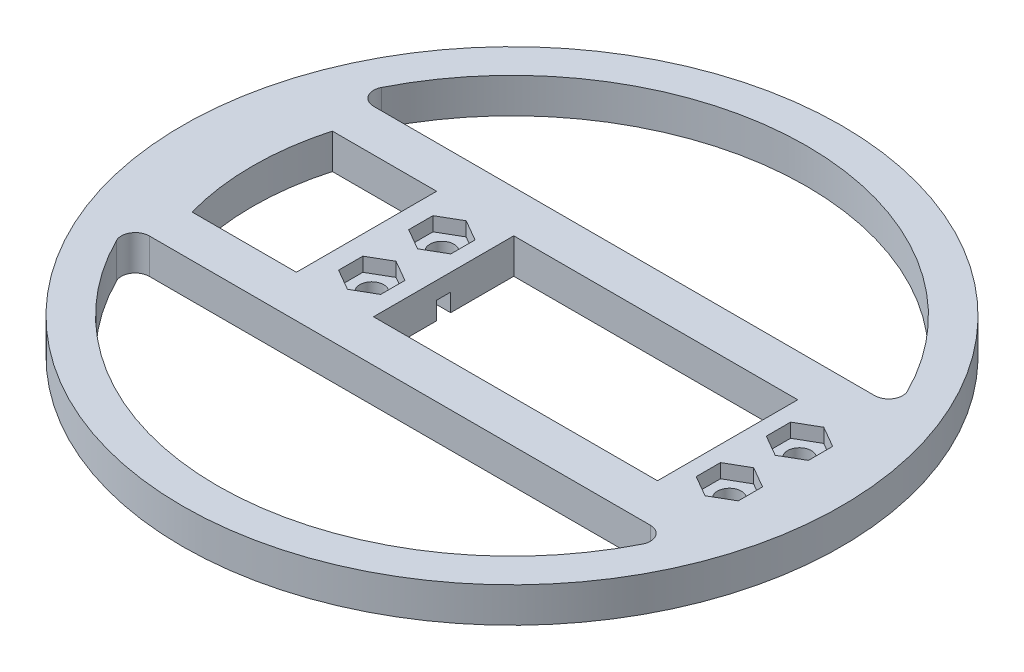
SolidWorks part; units mm, degrees
ref_plane "Front" through (0, 0, 0) normal (0, 0, 1) x (1, 0, 0)
ref_plane "Top" through (0, 0, 0) normal (0, 1, 0) x (1, 0, 0)
ref_plane "Right" through (0, 0, 0) normal (1, 0, 0) x (0, 0, -1)
sketch "Эскиз1" plane through (0, 0, 0) normal (0, 1, 0) x (1, 0, 0)
  line L0 (-47, 0) -> (47, 0) construction
  line L1 (10.5, 10) -> (10.5, -10) construction
  line L2 (-9.75, 10) -> (30.75, 10)
  line L3 (-9.75, 10) -> (-9.75, -10)
  line L4 (-9.75, -10) -> (30.75, -10)
  line L5 (30.75, 10) -> (30.75, -10)
  circle A0 centre (0, 0) radius 47
  circle A1 centre (-15, 5) radius 1.7
  circle A2 centre (-15, -5) radius 1.7
  circle A3 centre (36, 5) radius 1.7
  circle A4 centre (36, -5) radius 1.7
  dimension "D1" = 94
  dimension "D7" = 3.4
  dimension "D2" = 20
  dimension "D3" = 40.5
  dimension "D4" = 9.75
  dimension "D5" = 10
  dimension "D6" = 51
extrude "Бобышка-Вытянуть1" add sketch "Эскиз1" along normal blind 5
sketch "Эскиз2" plane through (0, 5, 0) normal (0, 1, 0) x (1, 0, 0)
  line L1 (-12, 6.7321) -> (-15, 8.4641)
  line L2 (-15, 8.4641) -> (-18, 6.7321)
  line L3 (-18, 6.7321) -> (-18, 3.2679)
  line L4 (-18, 3.2679) -> (-15, 1.5359)
  line L5 (-15, 1.5359) -> (-12, 3.2679)
  line L6 (-12, 3.2679) -> (-12, 6.7321)
  line L7 (-12, -3.2679) -> (-15, -1.5359)
  line L8 (-15, -1.5359) -> (-18, -3.2679)
  line L9 (-18, -3.2679) -> (-18, -6.7321)
  line L10 (-18, -6.7321) -> (-15, -8.4641)
  line L11 (-15, -8.4641) -> (-12, -6.7321)
  line L12 (-12, -6.7321) -> (-12, -3.2679)
  line L13 (36, 8.4641) -> (33, 6.7321)
  line L14 (33, 6.7321) -> (33, 3.2679)
  line L15 (33, 3.2679) -> (36, 1.5359)
  line L16 (36, 1.5359) -> (39, 3.2679)
  line L17 (39, 3.2679) -> (39, 6.7321)
  line L18 (39, 6.7321) -> (36, 8.4641)
  line L19 (36, -1.5359) -> (33, -3.2679)
  line L20 (33, -3.2679) -> (33, -6.7321)
  line L21 (33, -6.7321) -> (36, -8.4641)
  line L22 (36, -8.4641) -> (39, -6.7321)
  line L23 (39, -6.7321) -> (39, -3.2679)
  line L24 (39, -3.2679) -> (36, -1.5359)
  circle A0 centre (-15, 5) radius 3 construction
  circle A1 centre (-15, -5) radius 3 construction
  circle A2 centre (36, 5) radius 3 construction
  circle A3 centre (36, -5) radius 3 construction
  dimension "D1" = 6
extrude "Вырез-Вытянуть1" cut sketch "Эскиз2" against normal blind 2
sketch "Эскиз3" plane through (0, 0, 0) normal (0, 0, 1) x (1, 0, 0)
  line L0 (-9.75, 0) -> (30.75, 0) construction
  line L1 (-9.75, 0) -> (38.3089, 0)
  line L2 (-9.75, 0) -> (-17.3089, 0)
  line L3 (-17.3089, 0) -> (-6.4121, 3.6707)
  line L4 (-6.4121, 3.6707) -> (-9.75, 0)
  line L5 (10.5, 0) -> (10.5, 4.8258)
  line L6 (27.4121, 3.6707) -> (30.75, 0)
  line L7 (38.3089, 0) -> (27.4121, 3.6707)
extrude "Вырез-Вытянуть2" cut sketch "Эскиз3" against normal mid plane 2 contours L1 L7 L6 | L4 L3 L2
sketch "Эскиз4" plane through (0, 5, 0) normal (0, 1, 0) x (1, 0, 0)
  line L0 (-9.75, -10) -> (30.75, -10) construction
  line L1 (-9.75, -10) -> (30.75, -10)
  line L2 (30.75, 10) -> (-9.75, 10) construction
  line L3 (30.75, 10) -> (-9.75, 10)
  line L4 (47, 0) -> (-47, 0) construction
  line L5 (38.833, -16) -> (-38.833, -16)
  line L6 (38.833, 16) -> (-38.833, 16)
  line L7 (-20.75, -10) -> (-20.75, 10)
  line L8 (-20.75, 10) -> (-35.623, 10)
  line L9 (-20.75, -10) -> (-35.623, -10)
  line L10 (-9.75, 10) -> (-9.75, -10) construction
  circle A0 centre (0, 0) radius 47 construction
  circle A1 centre (0, 0) radius 47
  circle A2 centre (0, 0) radius 42
  arc A3 (-35.623, -10) -> (-35.623, 10) centre (0, 0) cw
  dimension "D1" = 84
  dimension "D4" = 37
  dimension "D2" = 6
  dimension "D3" = 11
extrude "Вырез-Вытянуть3" cut sketch "Эскиз4" against normal through all contours L5 A2 | L6 A2 | L4 L7 L8 A3 | L7 L4 A3 L9
fillet "Скругление1" radius 2 4 edges at (38.833, 2.5, -16) (-38.833, 2.5, -16) (-38.833, 2.5, 16) (38.833, 2.5, 16)
